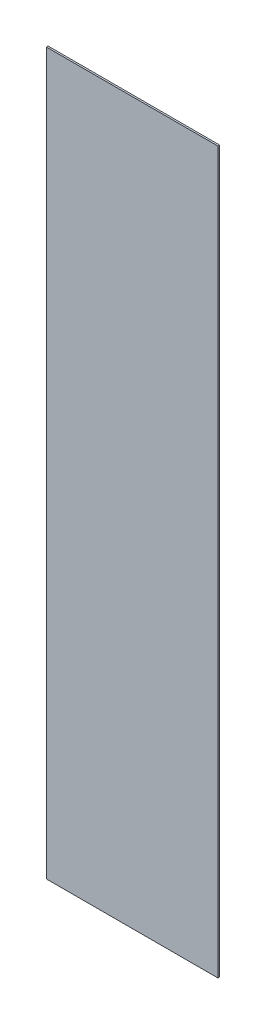
SolidWorks part; units mm, degrees
material "Kupfer"
ref_plane "Ebene vorne" through (0, 0, 0) normal (0, 0, 1) x (1, 0, 0)
ref_plane "Ebene oben" through (0, 0, 0) normal (0, 1, 0) x (1, 0, 0)
ref_plane "Ebene rechts" through (0, 0, 0) normal (1, 0, 0) x (0, 0, -1)
sketch "Skizze1" plane through (0, 0, 0) normal (0, 0, 1) x (1, 0, 0)
  line L1 (-25, 105) -> (25, 105)
  line L2 (-25, 105) -> (-25, -105)
  line L3 (-25, -105) -> (25, -105)
  line L4 (25, 105) -> (25, -105)
  line L5 (-25, 105) -> (25, -105) construction
  line L6 (-25, -105) -> (25, 105) construction
  point P0 (0, 0)
  dimension "D1" = 50
  dimension "D2" = 210
extrude "Aufsatz-Linear austragen1" add sketch "Skizze1" along normal blind 0.5
